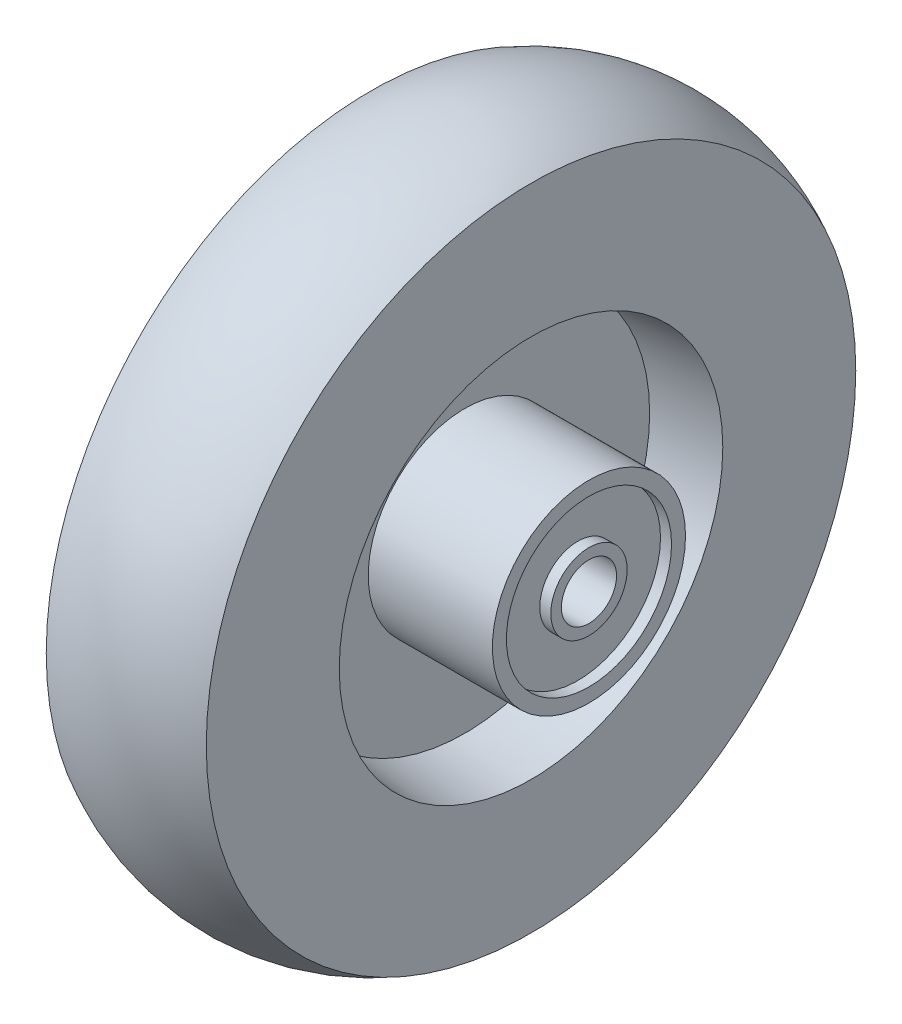
SolidWorks part; units mm, degrees
ref_plane "Front Plane" through (0, 0, 0) normal (0, 0, 1) x (1, 0, 0)
ref_plane "Top Plane" through (0, 0, 0) normal (0, 1, 0) x (1, 0, 0)
ref_plane "Right Plane" through (0, 0, 0) normal (1, 0, 0) x (0, 0, -1)
sketch "Sketch1" plane through (0, 0, 0) normal (0, 1, 0) x (1, 0, 0)
  line L0 (0, 115.5148) -> (0, 79.375) construction
  line L1 (-31.75, 22.225) -> (-31.75, 0)
  line L2 (-3.175, 22.225) -> (-31.75, 22.225)
  line L3 (18.415, 74.7374) -> (18.415, 44.1361)
  line L4 (-3.175, 42.545) -> (-18.415, 44.1361)
  line L5 (3.175, 42.545) -> (3.175, 22.225)
  line L6 (3.175, 22.225) -> (31.75, 22.225)
  line L7 (31.75, 22.225) -> (31.75, 0)
  line L8 (-31.75, 0) -> (-40.1263, 0) construction
  line L9 (-3.175, 42.545) -> (-3.175, 22.225)
  line L11 (-18.415, 74.7374) -> (-18.415, 44.1361)
  line L12 (31.75, 0) -> (-31.75, 0)
  line L14 (0, -79.375) -> (0, -1082.8998) construction
  line L15 (3.175, 42.545) -> (18.415, 44.1361)
  arc A0 (18.415, 74.7374) -> (-18.415, 74.7374) centre (0, 40.4948) ccw
  point P15 (31.75, 0)
  dimension "D1" = 158.75
  dimension "D2" = 79.375
  dimension "D3" = 31.75
  dimension "D6" = 20.32
  dimension "D7" = 28.575
revolve "Revolve1" add sketch "Sketch1" angle 360 about L8
sketch "Sketch2" plane through (31.75, 0, 0) normal (1, 0, 0) x (0, 0, -1)
  circle A1 centre (0, 0) radius 8.7883
  circle A2 centre (0, 0) radius 19.0018
extrude "Cut-Extrude1" cut sketch "Sketch2" against normal blind 2.54
sketch "Sketch3" plane through (31.75, 0, 0) normal (1, 0, 0) x (0, 0, -1)
  circle A0 centre (0, 0) radius 6.35
  dimension "D1" = 12.7
extrude "Cut-Extrude2" cut sketch "Sketch3" against normal through all
mirror "Mirror3" about plane through (0, 0, 0) normal (1, 0, 0) of "Cut-Extrude1"
